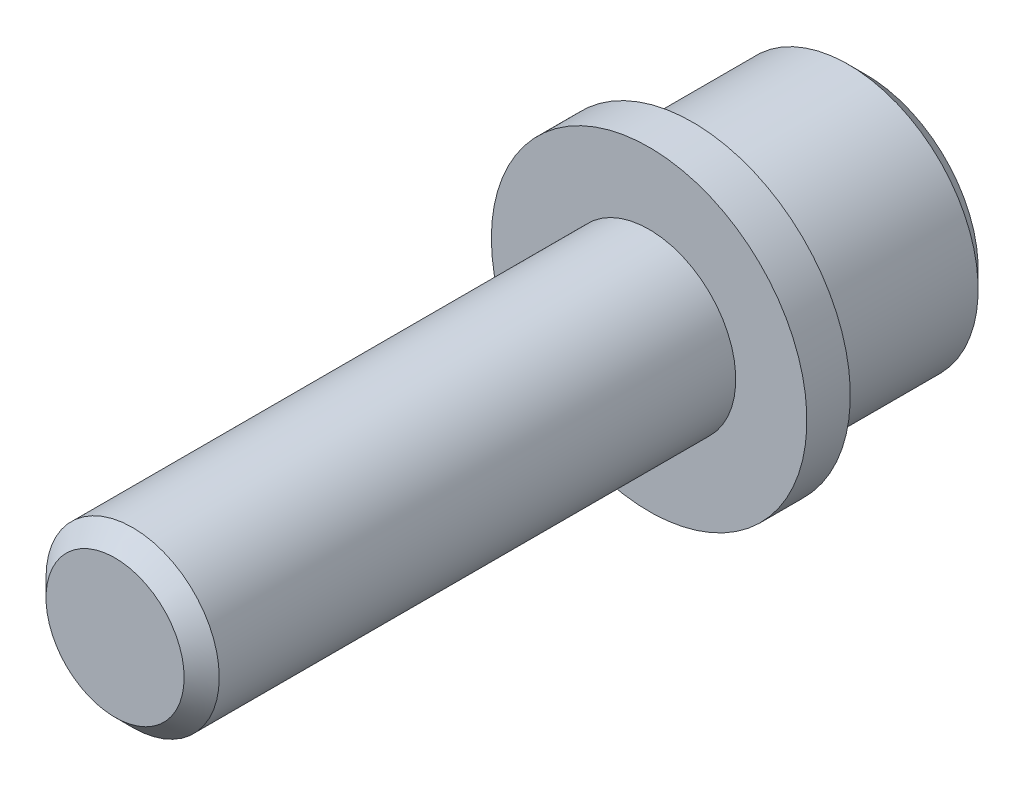
SolidWorks part; units mm, degrees
ref_plane "Front Plane" through (0, 0, 0) normal (0, 0, 1) x (1, 0, 0)
ref_plane "Top Plane" through (0, 0, 0) normal (0, 1, 0) x (1, 0, 0)
ref_plane "Right Plane" through (0, 0, 0) normal (1, 0, 0) x (0, 0, -1)
sketch "Sketch1" plane through (0, 0, 0) normal (0, 1, 0) x (1, 0, 0)
  line L0 (0, 86.6033) -> (0, -88.1227) construction
  line L1 (0, 52.8302) -> (0, 11.5552)
  line L2 (0, 11.5552) -> (-4.7625, 11.5552)
  line L3 (-4.7625, 11.5552) -> (-4.7625, 40.9176)
  line L4 (-4.7625, 40.9176) -> (-8.6741, 40.9176)
  line L5 (-8.6741, 40.9176) -> (-8.6741, 43.3052)
  line L6 (-8.6741, 43.3052) -> (-7.1437, 43.3052)
  line L7 (-7.1437, 43.3052) -> (-7.1437, 52.8302)
  line L8 (-7.1437, 52.8302) -> (0, 52.8302)
  point P10 (0, 0)
  point P13 (0, 0)
  dimension "D1" = 2.3876
  dimension "D2" = 41.275
  dimension "D3" = 9.525
  dimension "D4" = 14.2875
  dimension "D5" = 9.525
  dimension "D6" = 17.3482
revolve "Revolve1" add sketch "Sketch1" angle 360 about L0
sketch "Sketch2" plane through (0, 0, -52.8302) normal (0, 0, -1) x (-1, 0, 0)
  line L1 (2.273, 3.937) -> (-2.273, 3.937)
  line L2 (-2.273, 3.937) -> (-4.5461, 0)
  line L3 (-4.5461, 0) -> (-2.273, -3.937)
  line L4 (-2.273, -3.937) -> (2.273, -3.937)
  line L5 (2.273, -3.937) -> (4.5461, 0)
  line L6 (4.5461, 0) -> (2.273, 3.937)
  circle A0 centre (0, 0) radius 3.937 construction
  dimension "D1" = 7.874
extrude "Cut-Extrude1" cut sketch "Sketch2" against normal blind 6.35
chamfer "Chamfer1" distance 0.9652 angle 45 1 edges at (-4.7625, 0, -11.5552)
chamfer "Chamfer2" distance 0.9652 angle 45 1 edges at (-7.1437, 0, -52.8302)
